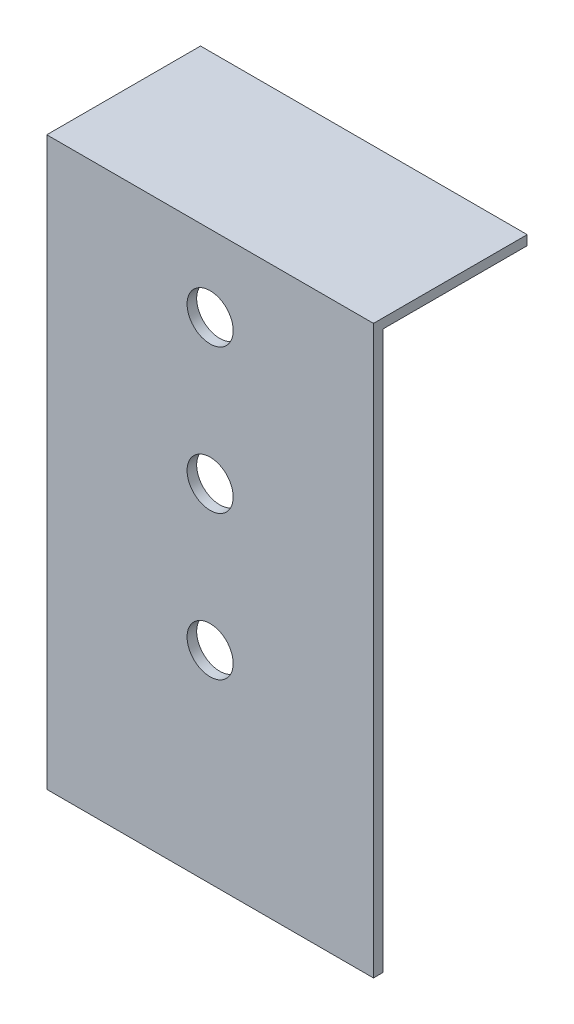
SolidWorks part; units mm, degrees
material "PPE"
ref_plane "Front Plane" through (0, 0, 0) normal (0, 0, 1) x (1, 0, 0)
ref_plane "Top Plane" through (0, 0, 0) normal (0, 1, 0) x (1, 0, 0)
ref_plane "Right Plane" through (0, 0, 0) normal (1, 0, 0) x (0, 0, -1)
sketch "Sketch1" plane through (0, 0, 0) normal (0, 1, 0) x (1, 0, 0)
  line L1 (-43.18, -1.27) -> (43.18, -1.27)
  line L2 (-43.18, -1.27) -> (-43.18, 1.27)
  line L3 (-43.18, 1.27) -> (43.18, 1.27)
  line L4 (43.18, -1.27) -> (43.18, 1.27)
  line L5 (-43.18, -1.27) -> (43.18, 1.27) construction
  line L6 (-43.18, 1.27) -> (43.18, -1.27) construction
  point P0 (0, 0)
  dimension "D1" = 86.36
  dimension "D2" = 2.54
extrude "Boss-Extrude1" add sketch "Sketch1" along normal blind 149.86
sketch "Sketch2" plane through (0, 0, -1.27) normal (0, 0, -1) x (-1, 0, 0)
  line L0 (43.18, 149.86) -> (43.18, 0) construction
  line L1 (-43.18, 149.86) -> (43.18, 149.86)
  line L2 (-43.18, 149.86) -> (-43.18, 147.32)
  line L3 (-43.18, 147.32) -> (43.18, 147.32)
  line L4 (43.18, 149.86) -> (43.18, 147.32)
  dimension "D1" = 2.54
extrude "Boss-Extrude2" add sketch "Sketch2" along normal blind 38.1
sketch "Sketch3" plane through (0, 0, 1.27) normal (0, 0, 1) x (1, 0, 0)
  circle A0 centre (0, 129.6554) radius 6.096
  circle A1 centre (0, 91.5554) radius 6.096
  circle A2 centre (0, 53.4554) radius 6.096
  dimension "D1" = 12.192
  dimension "D2" = 3
extrude "Cut-Extrude1" cut sketch "Sketch3" against normal through all
scale "Scale1" [suppressed]
